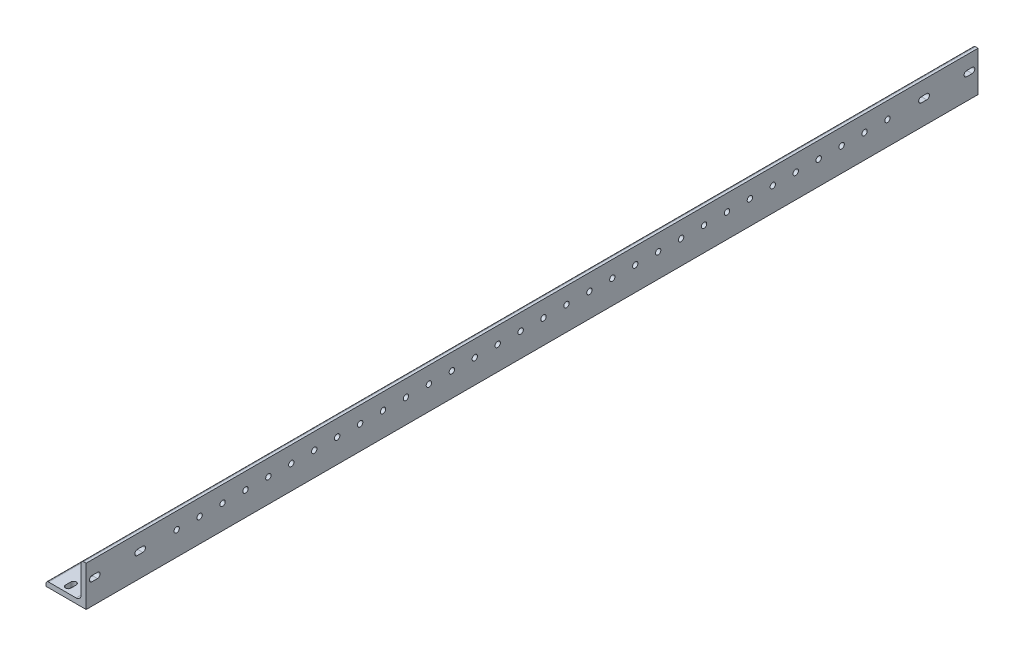
SolidWorks part; units mm, degrees
ref_plane "Front Plane" through (0, 0, 0) normal (0, 0, 1) x (1, 0, 0)
ref_plane "Top Plane" through (0, 0, 0) normal (0, 1, 0) x (1, 0, 0)
ref_plane "Right Plane" through (0, 0, 0) normal (1, 0, 0) x (0, 0, -1)
sketch "Sketch0" plane through (0, 0, 0) normal (0, 0, 1) x (1, 0, 0)
  line L0 (-12.7, -12.7) -> (12.7, -12.7)
  line L1 (12.7, -12.7) -> (12.7, 12.7)
  line L2 (12.7, 0) -> (0, 0) construction
  line L3 (0, 0) -> (0, -12.7) construction
  line L4 (9.525, -6.35) -> (9.525, 12.7) construction
  line L5 (6.35, -9.525) -> (-12.7, -9.525) construction
  arc A0 (9.525, -6.35) -> (6.35, -9.525) centre (6.35, -6.35) cw
  point P3 (8.5951, -8.5951)
  dimension "Inside Corner Radius" = 3.175
  dimension "Outside Height" = 25.4
  dimension "Inside Height" = 22.225
  dimension "Inside Width" = 22.225
  dimension "Wall Thickness" = 3.175
  dimension "D1" = 3.175
  dimension "Outside Width" = 25.4
sketch "Sketch1" plane through (0, 0, 0) normal (1, 0, 0) x (0, 0, -1)
  line L0 (609.6, 0) -> (-609.6, 0)
  point P4 (0, 0)
  dimension "Length" = 1219.2
sketch "Sketch2" plane through (0, 0, 0) normal (0, 0, 1) x (1, 0, 0)
  line L0 (-12.7, -12.7) -> (12.7, -12.7)
  line L1 (12.7, -12.7) -> (12.7, 12.7)
  line L2 (12.7, 12.7) -> (9.525, 12.7) construction
  line L3 (9.525, 11.1125) -> (9.525, -6.35)
  line L4 (6.35, -9.525) -> (-11.1125, -9.525)
  line L5 (-12.7, -12.7) -> (-12.7, -9.525) construction
  line L6 (11.1125, 12.7) -> (12.7, 12.7)
  line L7 (-12.7, -11.1125) -> (-12.7, -12.7)
  line L8 (12.7, 0) -> (0, 0) construction
  line L9 (0, 0) -> (0, -12.7) construction
  arc A0 (9.525, 11.1125) -> (11.1125, 12.7) centre (11.1125, 11.1125) cw
  arc A1 (-12.7, -11.1125) -> (-11.1125, -9.525) centre (-11.1125, -11.1125) cw
  arc A2 (9.525, -6.35) -> (6.35, -9.525) centre (6.35, -6.35) cw
  dimension "Inside Radius" = 3.175
  dimension "Height" = 25.4
  dimension "Width" = 25.4
  dimension "Thickness" = 3.175
extrude "Boss-Extrude1" add sketch "Sketch2" along normal mid plane 1219.2
sketch "Break Locations" plane through (0, 0, 0) normal (1, 0, 0) x (0, 0, -1)
  line L0 (-583.692, 0) -> (583.692, 0)
  line L1 (-609.6, -12.7) -> (-609.6, 12.7) construction
  line L2 (609.6, -12.7) -> (609.6, 12.7) construction
  point P0 (-588.01, 0)
  point P1 (588.01, 0)
  point P10 (0, 0)
  point P11 (583.692, 0)
  point P13 (-583.692, 0)
  dimension "D1" = 21.59
  dimension "D2" = 21.59
  dimension "D3" = 25.908
sketch "Sketch3" plane through (12.7, 0, 0) normal (1, 0, 0) x (0, 0, -1)
  line L0 (-609.6, -12.7) -> (609.6, -12.7) construction
  line L1 (609.6, 12.7) -> (-45.6, 12.7)
  line L2 (609.6, 12.7) -> (609.6, -12.7)
  line L3 (609.6, -12.7) -> (-45.6, -12.7)
  line L4 (-45.6, 12.7) -> (-45.6, -12.7)
  line L5 (-609.6, -12.7) -> (-609.6, 12.7) construction
  dimension "D1" = 564
extrude "Cut-Extrude2" cut sketch "Sketch3" against normal blind 30.48
sketch "Sketch4" plane through (0, -9.525, 0) normal (0, 1, 0) x (1, 0, 0)
  line L0 (-11.1125, -92.4325) -> (6.35, -92.4325) construction
  line L1 (-11.1125, -609.6) -> (-11.1125, -45.6) construction
  line L2 (3.9675, -92.4325) -> (-8.7325, -92.4325) construction
  line L3 (6.35, -609.6) -> (6.35, -45.6) construction
  line L4 (-2.3812, -92.4325) -> (-2.3812, -562.7675) construction
  line L6 (-11.1125, -562.7675) -> (6.35, -562.7675) construction
  line L7 (-2.3812, -552.35) -> (-2.3812, -562.7675)
  line L8 (-2.3813, -102.85) -> (-2.3812, -92.4325)
  line L9 (-12.7, -635) -> (12.7, -635) construction
  circle A0 centre (-2.3812, -552.35) radius 1.7
  circle A1 centre (-2.3813, -537.85) radius 1.7
  circle A2 centre (-2.3813, -523.35) radius 1.7
  circle A3 centre (-2.3813, -508.85) radius 1.7
  circle A4 centre (-2.3813, -494.35) radius 1.7
  circle A5 centre (-2.3813, -479.85) radius 1.7
  circle A6 centre (-2.3813, -465.35) radius 1.7
  circle A7 centre (-2.3813, -450.85) radius 1.7
  circle A8 centre (-2.3813, -436.35) radius 1.7
  circle A9 centre (-2.3813, -421.85) radius 1.7
  circle A10 centre (-2.3813, -407.35) radius 1.7
  circle A11 centre (-2.3813, -392.85) radius 1.7
  circle A12 centre (-2.3813, -378.35) radius 1.7
  circle A13 centre (-2.3813, -363.85) radius 1.7
  circle A14 centre (-2.3813, -349.35) radius 1.7
  circle A15 centre (-2.3813, -334.85) radius 1.7
  circle A16 centre (-2.3813, -320.35) radius 1.7
  circle A17 centre (-2.3813, -305.85) radius 1.7
  circle A18 centre (-2.3813, -291.35) radius 1.7
  circle A19 centre (-2.3813, -276.85) radius 1.7
  circle A20 centre (-2.3813, -262.35) radius 1.7
  circle A21 centre (-2.3813, -247.85) radius 1.7
  circle A22 centre (-2.3813, -233.35) radius 1.7
  circle A23 centre (-2.3813, -218.85) radius 1.7
  circle A24 centre (-2.3813, -204.35) radius 1.7
  circle A25 centre (-2.3813, -189.85) radius 1.7
  circle A26 centre (-2.3813, -175.35) radius 1.7
  circle A27 centre (-2.3813, -160.85) radius 1.7
  circle A28 centre (-2.3813, -146.35) radius 1.7
  circle A29 centre (-2.3813, -131.85) radius 1.7
  circle A30 centre (-2.3813, -117.35) radius 1.7
  circle A31 centre (-2.3813, -102.85) radius 1.7
  dimension "D1" = 3.4
  dimension "D3" = 14.5
  dimension "D4" = 72.2325
  dimension "D2" = 32
extrude "Cut-Extrude4" cut sketch "Sketch4" against normal through all contours A0 | A1 | A2 | A3 | A4 | A5 | A6 | A7 | A8 | A9 | A10 | A11 | A12 | A13 | A14 | A15 | A16 | A17 | A18 | A19 | A20 | A21 | A22 | A23 | A24 | A25 | A26 | A27 | A28 | A29 | A30 | A31
sketch "Sketch7" plane through (9.525, 0, 0) normal (-1, 0, 0) x (0, 0, 1)
  line L0 (92.4325, 11.1125) -> (92.4325, -6.35) construction
  line L1 (562.7675, 11.1125) -> (562.7675, -6.35) construction
  line L2 (609.6, 11.1125) -> (45.6, 11.1125) construction
  line L4 (609.6, -6.35) -> (45.6, -6.35) construction
  line L5 (92.4325, 2.3812) -> (562.7675, 2.3812) construction
  line L7 (102.85, 2.3812) -> (92.4325, 2.3812)
  line L8 (552.35, 2.3812) -> (562.7675, 2.3812)
  line L9 (628.65, -12.7) -> (628.65, 147.3) construction
  line L10 (20.2, -12.7) -> (20.2, 147.3) construction
  circle A0 centre (552.35, 2.3812) radius 1.7
  circle A1 centre (537.85, 2.3812) radius 1.7
  circle A2 centre (523.35, 2.3812) radius 1.7
  circle A3 centre (508.85, 2.3812) radius 1.7
  circle A4 centre (494.35, 2.3812) radius 1.7
  circle A5 centre (479.85, 2.3812) radius 1.7
  circle A6 centre (465.35, 2.3812) radius 1.7
  circle A7 centre (450.85, 2.3812) radius 1.7
  circle A8 centre (436.35, 2.3812) radius 1.7
  circle A9 centre (421.85, 2.3812) radius 1.7
  circle A10 centre (407.35, 2.3812) radius 1.7
  circle A11 centre (392.85, 2.3812) radius 1.7
  circle A12 centre (378.35, 2.3812) radius 1.7
  circle A13 centre (363.85, 2.3812) radius 1.7
  circle A14 centre (349.35, 2.3812) radius 1.7
  circle A15 centre (334.85, 2.3812) radius 1.7
  circle A16 centre (320.35, 2.3812) radius 1.7
  circle A17 centre (305.85, 2.3812) radius 1.7
  circle A18 centre (291.35, 2.3812) radius 1.7
  circle A19 centre (276.85, 2.3812) radius 1.7
  circle A20 centre (262.35, 2.3812) radius 1.7
  circle A21 centre (247.85, 2.3812) radius 1.7
  circle A22 centre (233.35, 2.3812) radius 1.7
  circle A23 centre (218.85, 2.3812) radius 1.7
  circle A24 centre (204.35, 2.3812) radius 1.7
  circle A25 centre (189.85, 2.3812) radius 1.7
  circle A26 centre (175.35, 2.3812) radius 1.7
  circle A27 centre (160.85, 2.3812) radius 1.7
  circle A28 centre (146.35, 2.3812) radius 1.7
  circle A29 centre (131.85, 2.3812) radius 1.7
  circle A30 centre (117.35, 2.3812) radius 1.7
  circle A31 centre (102.85, 2.3812) radius 1.7
  dimension "D1" = 3.4
  dimension "D3" = 14.5
  dimension "D4" = 65.8825
  dimension "D5" = 72.2325
  dimension "D2" = 32
extrude "Cut-Extrude6" cut sketch "Sketch7" against normal through all
sketch "Sketch8" plane through (9.525, 0, 0) normal (-1, 0, 0) x (0, 0, 1)
  line L0 (49.3305, 2.3825) -> (52.7305, 2.3825) construction
  line L1 (49.3305, 4.0825) -> (52.7305, 4.0825)
  line L2 (49.3305, 0.6825) -> (52.7305, 0.6825)
  line L3 (78.0325, 2.3825) -> (81.4325, 2.3825) construction
  line L4 (78.0325, 4.0825) -> (81.4325, 4.0825)
  line L5 (78.0325, 0.6825) -> (81.4325, 0.6825)
  line L6 (573.7675, 2.3825) -> (577.1675, 2.3825) construction
  line L7 (573.7675, 4.0825) -> (577.1675, 4.0825)
  line L8 (573.7675, 0.6825) -> (577.1675, 0.6825)
  line L9 (602.4695, 2.3825) -> (605.8695, 2.3825) construction
  line L10 (602.4695, 4.0825) -> (605.8695, 4.0825)
  line L11 (602.4695, 0.6825) -> (605.8695, 0.6825)
  circle A0 centre (79.7325, 2.3825) radius 1.7 construction
  circle A1 centre (51.0305, 2.3825) radius 1.7 construction
  circle A2 centre (575.4675, 2.3825) radius 1.7 construction
  circle A3 centre (604.1695, 2.3825) radius 1.7 construction
  arc A4 (49.3305, 4.0825) -> (49.3305, 0.6825) centre (49.3305, 2.3825) ccw
  arc A5 (52.7305, 0.6825) -> (52.7305, 4.0825) centre (52.7305, 2.3825) ccw
  arc A6 (78.0325, 4.0825) -> (78.0325, 0.6825) centre (78.0325, 2.3825) ccw
  arc A7 (81.4325, 0.6825) -> (81.4325, 4.0825) centre (81.4325, 2.3825) ccw
  arc A8 (573.7675, 4.0825) -> (573.7675, 0.6825) centre (573.7675, 2.3825) ccw
  arc A9 (577.1675, 0.6825) -> (577.1675, 4.0825) centre (577.1675, 2.3825) ccw
  arc A10 (602.4695, 4.0825) -> (602.4695, 0.6825) centre (602.4695, 2.3825) ccw
  arc A11 (605.8695, 0.6825) -> (605.8695, 4.0825) centre (605.8695, 2.3825) ccw
  point P14 (51.0305, 2.3825)
  point P21 (79.7325, 2.3825)
  point P27 (575.4675, 2.3825)
  point P35 (604.1695, 2.3825)
  dimension "D1" = 3.4
extrude "Cut-Extrude7" cut sketch "Sketch8" against normal through all
sketch "Sketch9" plane through (0, -9.525, 0) normal (0, 1, 0) x (1, 0, 0)
  line L0 (-2.3825, -605.8695) -> (-2.3825, -602.4695) construction
  line L1 (-4.0825, -605.8695) -> (-4.0825, -602.4695)
  line L2 (-0.6825, -605.8695) -> (-0.6825, -602.4695)
  line L3 (-2.3825, -577.1675) -> (-2.3825, -573.7675) construction
  line L4 (-4.0825, -577.1675) -> (-4.0825, -573.7675)
  line L5 (-0.6825, -577.1675) -> (-0.6825, -573.7675)
  line L6 (-2.3825, -81.4325) -> (-2.3825, -78.0325) construction
  line L7 (-4.0825, -81.4325) -> (-4.0825, -78.0325)
  line L8 (-0.6825, -81.4325) -> (-0.6825, -78.0325)
  line L9 (-2.3825, -52.7305) -> (-2.3825, -49.3305) construction
  line L10 (-4.0825, -52.7305) -> (-4.0825, -49.3305)
  line L11 (-0.6825, -52.7305) -> (-0.6825, -49.3305)
  circle A0 centre (-2.3825, -604.1695) radius 1.7 construction
  circle A1 centre (-2.3825, -575.4675) radius 1.7 construction
  circle A2 centre (-2.3825, -51.0305) radius 1.7 construction
  circle A3 centre (-2.3825, -79.7325) radius 1.7 construction
  arc A4 (-4.0825, -605.8695) -> (-0.6825, -605.8695) centre (-2.3825, -605.8695) ccw
  arc A5 (-0.6825, -602.4695) -> (-4.0825, -602.4695) centre (-2.3825, -602.4695) ccw
  arc A6 (-4.0825, -577.1675) -> (-0.6825, -577.1675) centre (-2.3825, -577.1675) ccw
  arc A7 (-0.6825, -573.7675) -> (-4.0825, -573.7675) centre (-2.3825, -573.7675) ccw
  arc A8 (-4.0825, -81.4325) -> (-0.6825, -81.4325) centre (-2.3825, -81.4325) ccw
  arc A9 (-0.6825, -78.0325) -> (-4.0825, -78.0325) centre (-2.3825, -78.0325) ccw
  arc A10 (-4.0825, -52.7305) -> (-0.6825, -52.7305) centre (-2.3825, -52.7305) ccw
  arc A11 (-0.6825, -49.3305) -> (-4.0825, -49.3305) centre (-2.3825, -49.3305) ccw
  point P14 (-2.3825, -604.1695)
  point P21 (-2.3825, -575.4675)
  point P27 (-2.3825, -79.7325)
  point P34 (-2.3825, -51.0305)
  dimension "D1" = 3.4
extrude "Cut-Extrude8" cut sketch "Sketch9" against normal through all contours L2 A5 L1 A4 | L5 A7 L4 A6 | L8 A8 L7 A9 | L11 A11 L10 A10
equation "\"D1@Break Locations\" = .85 * \"Height@Sketch2\""
equation "\"D2@Break Locations\"=\"D1@Break Locations\""
equation "\"Thickness@Sketch2\" = \"Wall Thickness@Sketch0\""
equation "\"Height@Sketch2\" = \"Outside Height@Sketch0\""
equation "\"Width@Sketch2\" = \"Outside Width@Sketch0\""
equation "\"Inside Radius@Sketch2\" = \"Inside Corner Radius@Sketch0\""
equation "\"Length@Boss-Extrude1\" = \"Length@Sketch1\""
equation "\"D3@Break Locations\"=\"D2@Break Locations\"*1.2"
equation "\"D1@Sketch0\"=\"Wall Thickness@Sketch0\""
